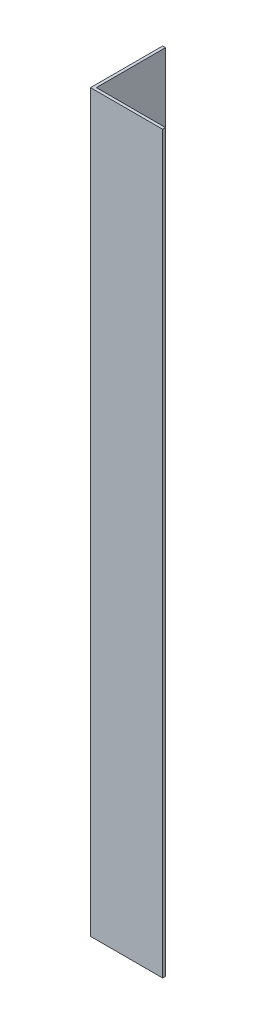
SolidWorks part; units mm, degrees
ref_plane "Front Plane" through (0, 0, 0) normal (0, 0, 1) x (1, 0, 0)
ref_plane "Top Plane" through (0, 0, 0) normal (0, 1, 0) x (1, 0, 0)
ref_plane "Right Plane" through (0, 0, 0) normal (1, 0, 0) x (0, 0, -1)
sketch "Sketch1" plane through (0, 0, 0) normal (0, 1, 0) x (1, 0, 0)
  line L1 (0, 0) -> (63.5, 0)
  line L2 (0, 0) -> (0, 63.5)
  line L3 (0, 63.5) -> (2.54, 63.5)
  line L4 (63.5, 0) -> (63.5, 2.54)
  line L7 (63.5, 2.54) -> (2.54, 2.54)
  line L8 (2.54, 63.5) -> (2.54, 2.54)
  dimension "D1" = 63.5
  dimension "D2" = 63.5
  dimension "D3" = 2.54
  dimension "D4" = 2.54
extrude "Boss-Extrude1" add sketch "Sketch1" along normal blind 647.7
